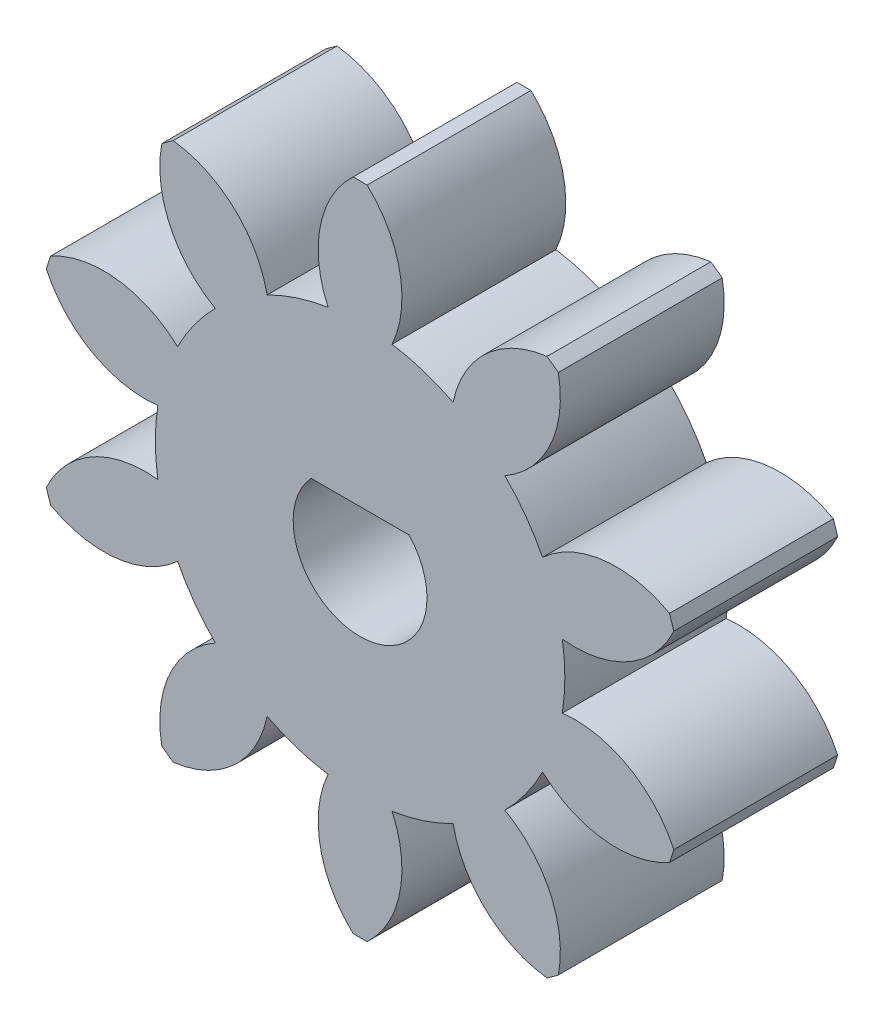
SolidWorks part; units mm, degrees
ref_plane "Front Plane" through (0, 0, 0) normal (0, 0, 1) x (1, 0, 0)
ref_plane "Top Plane" through (0, 0, 0) normal (0, 1, 0) x (1, 0, 0)
ref_plane "Right Plane" through (0, 0, 0) normal (1, 0, 0) x (0, 0, -1)
sketch "Sketch4" plane through (0, 0, 0) normal (0, 0, 1) x (1, 0, 0)
  point P0 (0, 12)
  arc B0 (11.3307, 3.9517) -> (6.6819, 3.404) centre (9.3858, 0.4563) ccw
  arc B1 (6.6819, 3.404) -> (5.3022, 5.303) centre (0, 0) ccw
  arc B2 (5.3022, 5.303) -> (7.2596, 9.555) centre (3.3343, 8.7855) ccw
  arc B3 (7.2596, 9.555) -> (6.844, 9.857) centre (0, 0) ccw
  arc B4 (6.844, 9.857) -> (3.405, 6.6814) centre (7.3251, 5.886) ccw
  arc B5 (3.405, 6.6814) -> (1.1725, 7.4068) centre (0, 0) ccw
  arc B6 (1.1725, 7.4068) -> (0.2569, 11.9973) centre (-2.4664, 9.0675) ccw
  arc B7 (0.2569, 11.9973) -> (-0.2569, 11.9973) centre (0, 0) ccw
  arc B8 (-0.2569, 11.9973) -> (-1.1725, 7.4068) centre (2.4664, 9.0675) ccw
  arc B9 (-1.1725, 7.4068) -> (-3.405, 6.6814) centre (0, 0) ccw
  arc B10 (-3.405, 6.6814) -> (-6.844, 9.857) centre (-7.3251, 5.886) ccw
  arc B11 (-6.844, 9.857) -> (-7.2596, 9.555) centre (0, 0) ccw
  arc B12 (-7.2596, 9.555) -> (-5.3022, 5.303) centre (-3.3343, 8.7855) ccw
  arc B13 (-5.3022, 5.303) -> (-6.6819, 3.404) centre (0, 0) ccw
  arc B14 (-6.6819, 3.404) -> (-11.3307, 3.9517) centre (-9.3858, 0.4563) ccw
  arc B15 (-11.3307, 3.9517) -> (-11.4894, 3.463) centre (0, 0) ccw
  arc B16 (-11.4894, 3.463) -> (-7.4066, 1.1737) centre (-7.8615, 5.1477) ccw
  arc B17 (-7.4066, 1.1737) -> (-7.4066, -1.1737) centre (0, 0) ccw
  arc B18 (-7.4066, -1.1737) -> (-11.4894, -3.463) centre (-7.8615, -5.1477) ccw
  arc B19 (-11.4894, -3.463) -> (-11.3307, -3.9517) centre (0, 0) ccw
  arc B20 (-11.3307, -3.9517) -> (-6.6819, -3.404) centre (-9.3858, -0.4563) ccw
  arc B21 (-6.6819, -3.404) -> (-5.3022, -5.303) centre (0, 0) ccw
  arc B22 (-5.3022, -5.303) -> (-7.2596, -9.555) centre (-3.3343, -8.7855) ccw
  arc B23 (-7.2596, -9.555) -> (-6.844, -9.857) centre (0, 0) ccw
  arc B24 (-6.844, -9.857) -> (-3.405, -6.6814) centre (-7.3251, -5.886) ccw
  arc B25 (-3.405, -6.6814) -> (-1.1725, -7.4068) centre (0, 0) ccw
  arc B26 (-1.1725, -7.4068) -> (-0.2569, -11.9973) centre (2.4664, -9.0675) ccw
  arc B27 (-0.2569, -11.9973) -> (0.2569, -11.9973) centre (0, 0) ccw
  arc B28 (0.2569, -11.9973) -> (1.1725, -7.4068) centre (-2.4664, -9.0675) ccw
  arc B29 (1.1725, -7.4068) -> (3.405, -6.6814) centre (0, 0) ccw
  arc B30 (3.405, -6.6814) -> (6.844, -9.857) centre (7.3251, -5.886) ccw
  arc B31 (6.844, -9.857) -> (7.2596, -9.555) centre (0, 0) ccw
  arc B32 (7.2596, -9.555) -> (5.3022, -5.303) centre (3.3343, -8.7855) ccw
  arc B33 (5.3022, -5.303) -> (6.6819, -3.404) centre (0, 0) ccw
  arc B34 (6.6819, -3.404) -> (11.3307, -3.9517) centre (9.3858, -0.4563) ccw
  arc B35 (11.3307, -3.9517) -> (11.4894, -3.463) centre (0, 0) ccw
  arc B36 (11.4894, -3.463) -> (7.4066, -1.1737) centre (7.8615, -5.1477) ccw
  arc B37 (7.4066, -1.1737) -> (7.4066, 1.1737) centre (0, 0) ccw
  arc B38 (7.4066, 1.1737) -> (11.4894, 3.463) centre (7.8615, 5.1477) ccw
  arc B39 (11.4894, 3.463) -> (11.3307, 3.9517) centre (0, 0) ccw
  circle B40 centre (0, 0) radius 2
sketch_block_instance "Block3-1"
sketch_block "Block3"
extrude "Boss-Extrude3" add sketch "Sketch4" along normal blind 6
sketch "Sketch6" plane through (0, 0, 6) normal (0, 0, 1) x (1, 0, 0)
  circle A0 centre (0, 0) radius 3.2769
extrude "Boss-Extrude4" add sketch "Sketch6" against normal up to surface (6 mm away) up to face at (0, 0, 0)
sketch "Sketch7" plane through (0, 0, 6) normal (0, 0, 1) x (1, 0, 0)
  line L0 (0, 0) -> (0, 1.62) construction
  line L2 (-1.7927, 1.67) -> (1.7927, 1.67)
  arc A0 (-1.7927, 1.67) -> (1.7927, 1.67) centre (0, 0) ccw
  dimension "D1" = 1.67
extrude "Cut-Extrude1" cut sketch "Sketch7" against normal blind 10
